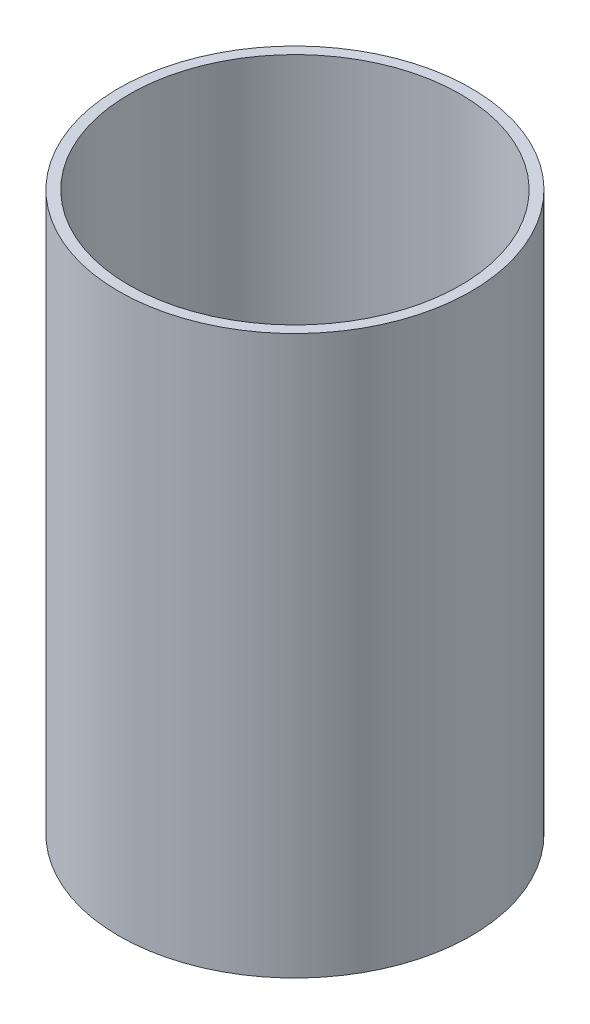
SolidWorks part; units mm, degrees
ref_plane "Front Plane" through (0, 0, 0) normal (0, 0, 1) x (1, 0, 0)
ref_plane "Top Plane" through (0, 0, 0) normal (0, 1, 0) x (1, 0, 0)
ref_plane "Right Plane" through (0, 0, 0) normal (1, 0, 0) x (0, 0, -1)
sketch "Sketch1" plane through (0, 0, 0) normal (0, 1, 0) x (1, 0, 0)
  circle A0 centre (0, 0) radius 25.175
  circle A1 centre (0, 0) radius 23.675
  dimension "D1" = 50.35
  dimension "D2" = 47.35
extrude "Boss-Extrude1" add sketch "Sketch1" along normal blind 79.8
